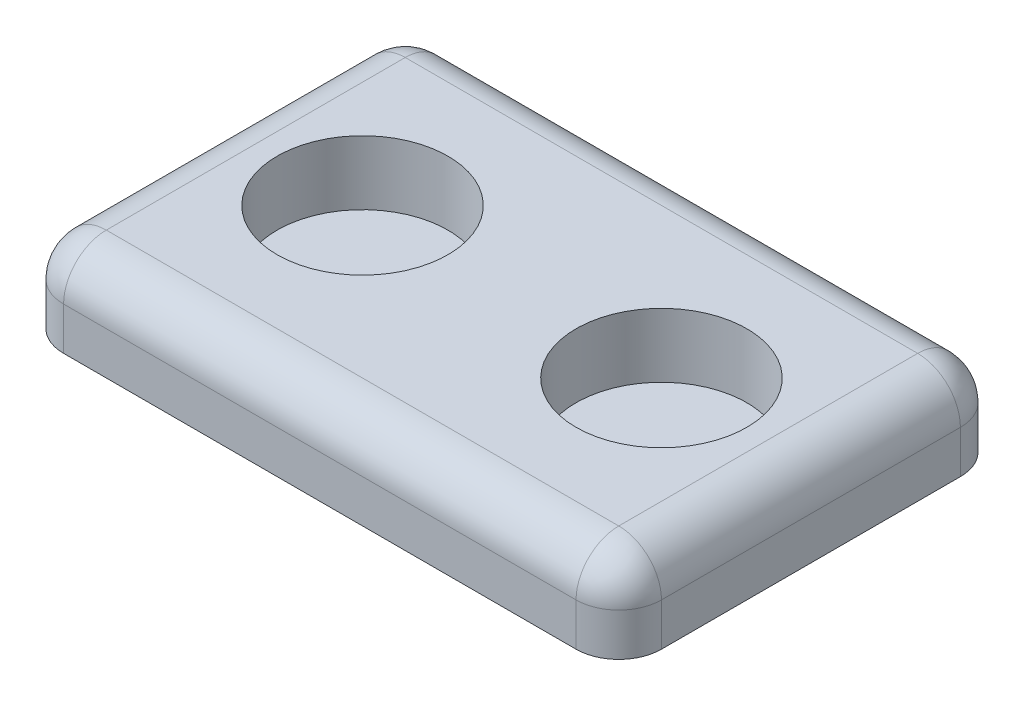
SolidWorks part; units mm, degrees
ref_plane "Front Plane" through (0, 0, 0) normal (0, 0, 1) x (1, 0, 0)
ref_plane "Top Plane" through (0, 0, 0) normal (0, 1, 0) x (1, 0, 0)
ref_plane "Right Plane" through (0, 0, 0) normal (1, 0, 0) x (0, 0, -1)
sketch "Sketch1" plane through (0, 0, 0) normal (0, 1, 0) x (1, 0, 0)
  line L1 (70, -45) -> (-70, -45)
  line L2 (70, -45) -> (70, 45)
  line L3 (70, 45) -> (-70, 45)
  line L4 (-70, -45) -> (-70, 45)
  line L5 (70, -45) -> (-70, 45) construction
  line L6 (70, 45) -> (-70, -45) construction
  point P0 (0, 0)
  dimension "D1" = 90
  dimension "D2" = 140
extrude "Boss-Extrude1" add sketch "Sketch1" along normal blind 20
sketch "Sketch2" plane through (0, 20, 0) normal (0, 1, 0) x (1, 0, 0)
  line L0 (-35, 0) -> (35, 0) construction
  line L2 (-70, 45) -> (-70, -45) construction
  circle A0 centre (-35, 0) radius 20
  circle A1 centre (35, 0) radius 20
  dimension "D3" = 40
  dimension "D1" = 70
  dimension "D2" = 35
extrude "Cut-Extrude1" cut sketch "Sketch2" against normal blind 15
fillet "Fillet1" radius 10 4 edges at (70, 10, 45) (70, 10, -45) (-70, 10, -45) (-70, 10, 45)
fillet "Fillet2" radius 10 8 edges at (0, 20, 45) (-67.0711, 20, 42.0711) (-70, 20, 0) (-67.0711, 20, -42.0711) (0, 20, -45) (67.0711, 20, -42.0711) (70, 20, 0) (67.0711, 20, 42.0711)
